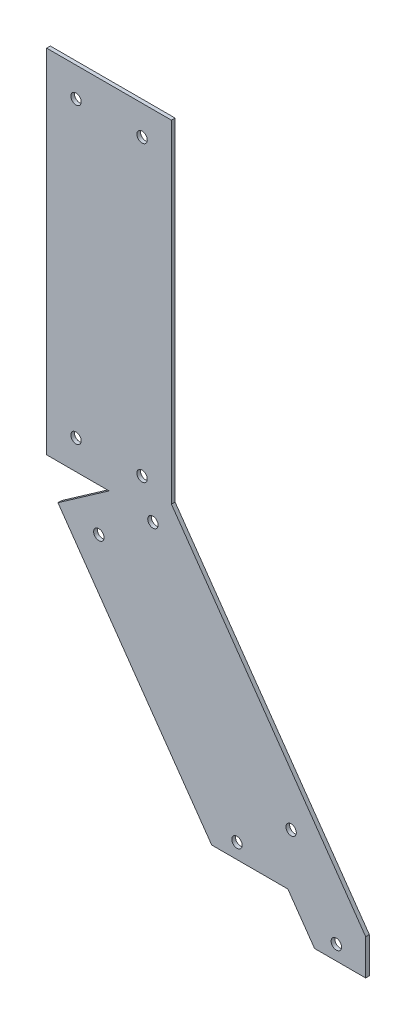
SolidWorks part; units mm, degrees
ref_plane "Front Plane" through (0, 0, 0) normal (0, 0, 1) x (1, 0, 0)
ref_plane "Top Plane" through (0, 0, 0) normal (0, 1, 0) x (1, 0, 0)
ref_plane "Right Plane" through (0, 0, 0) normal (1, 0, 0) x (0, 0, -1)
sketch "Sketch1" plane through (0, 0, 0) normal (0, 0, 1) x (1, 0, 0)
  line L0 (0, 0) -> (0, 152.4)
  line L1 (0, 0) -> (88.9264, -127)
  line L2 (88.9264, -127) -> (0, 0)
  line L3 (0, 152.4) -> (26.9875, 152.4)
  line L4 (0, 152.4) -> (0, 0)
  line L5 (0, 0) -> (26.9875, 0)
  line L6 (26.9875, 152.4) -> (26.9875, 0)
  line L7 (88.9264, -127) -> (111.0332, -111.5206)
  line L8 (0, 0) -> (22.1069, 15.4794)
  line L9 (111.0332, -111.5206) -> (22.1069, 15.4794)
  line L10 (0, 0) -> (88.9264, -127)
  line L11 (0, 152.4) -> (-26.9875, 152.4)
  line L12 (0, 152.4) -> (0, 0)
  line L13 (0, 0) -> (-26.9875, 0)
  line L14 (-26.9875, 152.4) -> (-26.9875, 0)
  line L15 (0, 0) -> (-22.1069, -15.4794)
  line L16 (88.9264, -127) -> (66.8195, -142.4794)
  line L17 (-22.1069, -15.4794) -> (66.8195, -142.4794)
  line L18 (-11.7036, -8.195) -> (77.2227, -135.195) construction
  line L19 (88.9264, -127) -> (111.0332, -127)
  line L20 (111.0332, -127) -> (111.0332, -111.5206)
  line L21 (44.4203, -110.49) -> (77.3659, -110.49)
  line L23 (111.0332, -127) -> (25.9165, -127) construction
  line L24 (111.0332, -127) -> (111.0332, -114.3) construction
  circle A0 centre (-14.2875, 139.7) radius 2.25
  circle A1 centre (-14.2875, 12.7) radius 2.25
  circle A2 centre (14.2875, 12.7) radius 2.25
  circle A3 centre (14.2875, 139.7) radius 2.25
  circle A4 centre (-4.4192, -18.5982) radius 2.25
  circle A5 centre (55.3695, -103.9853) radius 2.25
  circle A6 centre (78.7767, -87.5953) radius 2.25
  circle A7 centre (18.9881, -2.2083) radius 2.25
  circle A9 centre (98.3332, -120.65) radius 2.25
  dimension "D6" = 4.5
  dimension "D14" = 6.35
  dimension "D1" = 152.4
  dimension "D2" = 145
  dimension "D3" = 26.9875
  dimension "D4" = 127
  dimension "D5" = 12.7
  dimension "D7" = 12.7
  dimension "D8" = 12.7
  dimension "D9" = 12.7
  dimension "D10" = 12.7
  dimension "D11" = 38.1
  dimension "D12" = 16.51
  dimension "D13" = 12.7
extrude "Boss-Extrude1" add sketch "Sketch1" along normal blind 1.5875 contours L5 A7 L1 L10 L7 L9 L6 A6 | L19 L20 L7 | L17 L21 L1 L15 A5 A4 | L8 A2 L9 L6 L3 L0 A3 | L5 A7 L6 L9 L8 A2 | L11 L14 L13 L0 A1 A0
